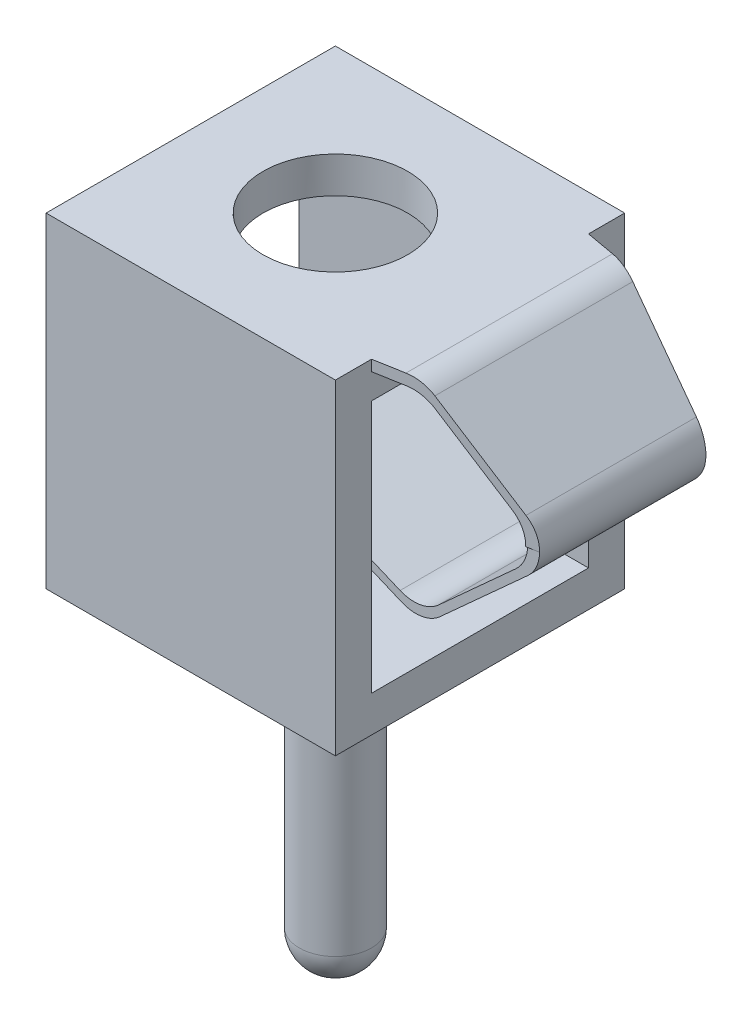
SolidWorks part; units mm, degrees
ref_plane "Front Plane" through (0, 0, 0) normal (0, 0, 1) x (1, 0, 0)
ref_plane "Top Plane" through (0, 0, 0) normal (0, 1, 0) x (1, 0, 0)
ref_plane "Right Plane" through (0, 0, 0) normal (1, 0, 0) x (0, 0, -1)
sketch "Sketch1" plane through (0, 0, 0) normal (1, 0, 0) x (0, 0, -1)
  line L1 (-2, 2.25) -> (2, 2.25)
  line L2 (-2, 2.25) -> (-2, -2.25)
  line L3 (-2, -2.25) -> (2, -2.25)
  line L4 (2, 2.25) -> (2, -2.25)
  line L5 (-2, 2.25) -> (2, -2.25) construction
  line L6 (-2, -2.25) -> (2, 2.25) construction
  line L7 (-1.5, 1.75) -> (1.5, 1.75)
  line L8 (-1.5, 1.75) -> (-1.5, -1.75)
  line L9 (-1.5, -1.75) -> (1.5, -1.75)
  line L10 (1.5, 1.75) -> (1.5, -1.75)
  line L11 (-1.5, 1.75) -> (1.5, -1.75) construction
  line L12 (-1.5, -1.75) -> (1.5, 1.75) construction
  point P0 (0, 0)
  point P6 (0, 0)
  dimension "D1" = 4.5
  dimension "D2" = 4
  dimension "D3" = 3
  dimension "D4" = 3.5
extrude "Boss-Extrude1" add sketch "Sketch1" along normal blind 4
sketch "Sketch2" plane through (0, -2.25, 0) normal (0, -1, 0) x (1, 0, 0)
  line L0 (4, 2) -> (0, 2) construction
  circle A0 centre (2, 0) radius 0.5
  point P2 (2, 2)
  dimension "D1" = 1
extrude "Boss-Extrude2" add sketch "Sketch2" along normal blind 4.55
fillet "Fillet1" radius 0.5 1 edges at (2, -6.8, -0.5)
sketch "Sketch3" plane through (0, 2.25, 0) normal (0, 1, 0) x (1, 0, 0)
  line L0 (4, 2) -> (0, 2) construction
  circle A0 centre (2, 0) radius 1
  point P2 (2, 2)
  dimension "D1" = 2
extrude "Cut-Extrude1" cut sketch "Sketch3" against normal blind 2.55
sketch "Sketch5" plane through (0, 0, 2) normal (0, 0, 1) x (1, 0, 0)
  line L0 (4, 2.25) -> (4.4039, 2.25)
  line L1 (-0.1, 2.25) -> (5.9, 2.25) construction
  line L2 (4.7438, 2.1167) -> (5.8132, 1.1253)
  line L3 (5.8089, 0.388) -> (4.5964, -0.7101)
  line L4 (4.0668, -0.8003) -> (1.5954, 0.2402)
  line L5 (4, 2.25) -> (4, 2.1)
  line L6 (4, 2.25) -> (4, -2.25) construction
  line L7 (4, 2.1) -> (4.4039, 2.1)
  line L8 (4.7438, 1.9667) -> (5.6504, 1.1262)
  line L9 (5.6461, 0.3889) -> (4.5745, -0.5815)
  line L10 (4.0449, -0.6718) -> (1.5954, 0.3596)
  line L11 (1.5954, 0.3596) -> (1.5954, 0.2402)
  arc A0 (4.4039, 2.25) -> (4.7438, 2.1167) centre (4.4039, 1.75) cw
  arc A1 (4.7438, 1.9667) -> (4.4039, 2.1) centre (4.4039, 1.6) ccw
  arc A2 (5.8132, 1.1253) -> (5.8089, 0.388) centre (5.4733, 0.7586) cw
  arc A3 (5.6461, 0.3889) -> (5.6504, 1.1262) centre (5.3104, 0.7595) ccw
  arc A4 (4.5964, -0.7101) -> (4.0668, -0.8003) centre (4.2608, -0.3395) cw
  arc A5 (4.5745, -0.5815) -> (4.0449, -0.6718) centre (4.2389, -0.2109) cw
  point P17 (4.6, 2.25)
  point P20 (4.6, 2.1)
  point P23 (6.2133, 0.7543)
  point P28 (4.3603, -0.9239)
  dimension "D11" = 0.5
  dimension "D1" = 0.6
  dimension "D2" = 0.15
  dimension "D3" = 0.11
  dimension "D4" = 0.11
  dimension "D5" = 0.11
  dimension "D6" = 85
  dimension "D7" = 2.2
  dimension "D8" = 115
  dimension "D9" = 3
  dimension "D10" = 2.5
extrude "Boss-Extrude3" add sketch "Sketch5" against normal up to surface (3 mm away) from offset 0.5 up to face at (2, 0, -1.5) offset against normal yes
sketch "Sketch6" plane through (0, 2.25, 0) normal (0, 1, 0) x (1, 0, 0)
  line L0 (4, 1.5) -> (5.9733, 1.15)
  line L1 (5.9733, -1.5) -> (5.9733, 1.5) construction
  line L2 (5.9733, 1.15) -> (5.9733, 1.5)
  line L3 (5.9733, 1.5) -> (5.8089, 1.5) construction
  line L4 (5.9733, 1.5) -> (4, 1.5)
  line L5 (4, -1.5) -> (5.9733, -1.15)
  line L6 (5.9733, -1.15) -> (5.9733, -1.5)
  line L7 (5.8089, -1.5) -> (5.9733, -1.5) construction
  line L8 (5.9733, -1.5) -> (4, -1.5)
  dimension "D1" = 0.35
extrude "Cut-Extrude2" cut sketch "Sketch6" against normal blind 1.5
sketch "Sketch7" plane through (4, 0, 0) normal (1, 0, 0) x (0, 0, -1)
  line L0 (-1.5, -0.7722) -> (-1.5, -1.75) construction
  line L1 (-1.15, 0.75) -> (-1.5, 0.75)
  line L2 (-1.15, 0.75) -> (-1.15, -1.25)
  line L3 (-1.15, -1.25) -> (-1.5, -1.25)
  line L4 (-1.5, 0.75) -> (-1.5, -1.25)
  line L5 (1.5, -1.75) -> (1.5, -0.7722) construction
  line L6 (1.15, 0.75) -> (1.5, 0.75)
  line L7 (1.15, 0.75) -> (1.15, -1.25)
  line L8 (1.15, -1.25) -> (1.5, -1.25)
  line L9 (1.5, 0.75) -> (1.5, -1.25)
  dimension "D1" = 2
extrude "Cut-Extrude3" cut sketch "Sketch7" against normal blind 7.5 and the other way blind 4.5
